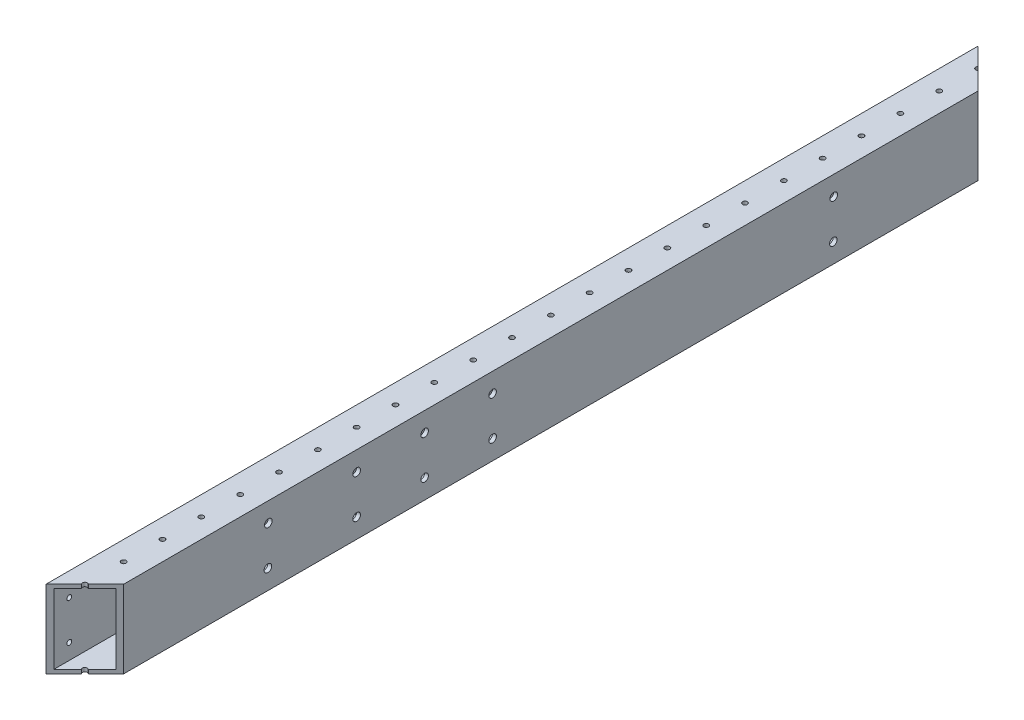
SolidWorks part; units mm, degrees
material "6061-T6 (SS)"
ref_plane "Front Plane" through (0, 0, 0) normal (0, 0, 1) x (1, 0, 0)
ref_plane "Top Plane" through (0, 0, 0) normal (0, 1, 0) x (1, 0, 0)
ref_plane "Right Plane" through (0, 0, 0) normal (1, 0, 0) x (0, 0, -1)
sketch "Sketch1" plane through (0, 0, 0) normal (0, 0, 1) x (1, 0, 0)
  line L1 (0, 0) -> (25.4, 0)
  line L2 (0, 0) -> (0, 50.8)
  line L3 (0, 50.8) -> (25.4, 50.8)
  line L4 (25.4, 0) -> (25.4, 50.8)
  dimension "D1" = 50.8
  dimension "D2" = 25.4
extrude "Extrude-Thin1" add sketch "Sketch1" along normal blind 609.6 thin thin type one direction reverse wall 2.54
sketch "Sketch2" plane through (0, 50.8, 0) normal (0, 1, 0) x (1, 0, 0)
  line L0 (12.7, -609.6) -> (12.7, -665.6007) construction
  line L1 (25.4, -609.6) -> (0, -609.6) construction
  circle A0 centre (12.7, -596.9) radius 1.5875
  dimension "D1" = 12.7
  dimension "D2" = 3.175
extrude "Cut-Extrude1" cut sketch "Sketch2" against normal through all
pattern_linear "LPattern1" count 50 spacing 25.4 along (0, 0, -1) of "Cut-Extrude1"
sketch "Sketch4" plane through (0, 50.8, 0) normal (0, 1, 0) x (1, 0, 0)
  line L0 (0, -609.6) -> (25.4, -584.2)
  line L1 (25.4, -609.6) -> (25.4, 0) construction
  line L2 (25.4, -584.2) -> (25.4, -609.6)
  line L3 (25.4, -609.6) -> (0, -609.6)
  line L4 (0, 0) -> (25.4, 0)
  line L5 (25.4, 0) -> (25.4, -25.4)
  line L6 (25.4, -25.4) -> (0, 0)
extrude "Cut-Extrude2" cut sketch "Sketch4" against normal through all
sketch "Sketch5" plane through (0, 0, 0) normal (-1, 0, 0) x (0, 0, 1)
  line L0 (304.8, 50.8) -> (304.8, 0) construction
  line L1 (609.6, 50.8) -> (0, 50.8) construction
  line L2 (609.6, 0) -> (0, 0) construction
  line L3 (12.7, 50.8) -> (12.7, 0) construction
  line L4 (584.2, 0) -> (25.4, 0) construction
  line L5 (0, 50.8) -> (0, 0) construction
  circle A0 centre (12.7, 12.7) radius 1.5875
  circle A1 centre (12.7, 38.1) radius 1.5875
  circle A2 centre (596.9, 38.1) radius 1.5875
  circle A3 centre (596.9, 12.7) radius 1.5875
  dimension "D1" = 3.175
  dimension "D3" = 25.4
  dimension "D2" = 12.7
  dimension "D4" = 12.7
extrude "Cut-Extrude3" cut sketch "Sketch5" against normal through all
sketch "Sketch7" plane through (0, 0, 0) normal (-1, 0, 0) x (0, 0, 1)
  circle A0 centre (489.585, 38.1) radius 2.4892 construction
  circle A1 centre (489.8452, 12.7) radius 2.4892 construction
  circle A2 centre (120.015, 12.7) radius 2.4892 construction
  circle A3 centre (119.7548, 38.1) radius 2.4892 construction
  circle A4 centre (342.9, 38.1) radius 2.4892 construction
  circle A5 centre (342.9, 12.7) radius 2.4892 construction
  circle A6 centre (387.35, 12.7) radius 2.4892 construction
  circle A7 centre (387.35, 38.1) radius 2.4892 construction
  circle A8 centre (431.8, 38.1) radius 2.4892 construction
  circle A9 centre (431.8, 12.7) radius 2.4892 construction
  circle A10 centre (489.585, 38.1) radius 2.4892
  circle A11 centre (489.8452, 12.7) radius 2.4892
  circle A12 centre (120.015, 12.7) radius 2.4892
  circle A13 centre (119.7548, 38.1) radius 2.4892
  circle A14 centre (342.9, 38.1) radius 2.4892
  circle A15 centre (342.9, 12.7) radius 2.4892
  circle A16 centre (387.35, 12.7) radius 2.4892
  circle A17 centre (387.35, 38.1) radius 2.4892
  circle A18 centre (431.8, 38.1) radius 2.4892
  circle A19 centre (431.8, 12.7) radius 2.4892
extrude "Cut-Extrude4" cut sketch "Sketch7" against normal through all
